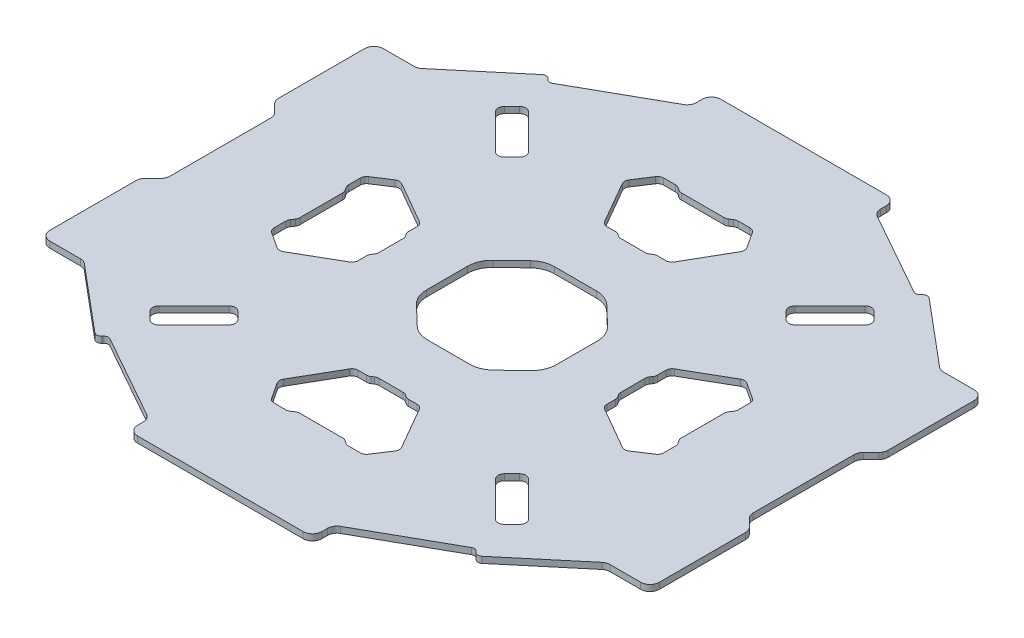
SolidWorks part; units mm, degrees
ref_plane "Piano frontale" through (0, 0, 0) normal (0, 0, 1) x (1, 0, 0)
ref_plane "Piano superiore" through (0, 0, 0) normal (0, 1, 0) x (1, 0, 0)
ref_plane "Piano destro" through (0, 0, 0) normal (1, 0, 0) x (0, 0, -1)
sketch "Schizzo3" plane through (0, 0, 0) normal (0, 1, 0) x (1, 0, 0)
  line L0 (-226.0625, 21.4509) -> (-226.0625, 53.9656)
  line L1 (-226.9412, 56.0869) -> (-229.4265, 58.5722)
  line L2 (-230.3052, 60.6935) -> (-230.3052, 88.4509)
  line L3 (-227.3052, 91.4509) -> (-217.3971, 91.4509)
  line L4 (-215.4687, 92.1528) -> (-194.4729, 109.7703)
  line L5 (-192.3597, 109.5854) -> (-192.1951, 109.3893)
  line L6 (-190.3111, 109.0459) -> (-163.2864, 124.2352)
  line L7 (-161.7563, 126.8504) -> (-161.7563, 128.7082)
  line L8 (-158.7563, 131.7082) -> (-105.3688, 131.7082)
  line L11 (-193.5625, 30.8043) -> (-193.5625, 44.6122)
  line L12 (-193.8889, 45.7071) -> (-194.5446, 46.7094)
  line L13 (-194.8709, 47.8043) -> (-194.8709, 51.6267)
  line L14 (-193.9658, 53.3003) -> (-188.7857, 56.689)
  line L15 (-186.6931, 56.7487) -> (-173.1597, 48.9588)
  line L16 (-172.1574, 47.2255) -> (-172.1574, 44.478)
  line L17 (-171.8311, 43.3831) -> (-171.3889, 42.7071)
  line L18 (-171.0625, 41.6122) -> (-171.0625, 33.8043)
  line L25 (-180.3244, 80.6668) -> (-191.6382, 91.9805)
  line L26 (-175.0211, 83.1417) -> (-177.496, 80.6668)
  line L27 (-186.3349, 97.2838) -> (-175.0211, 85.9701)
  line L28 (-191.6382, 94.809) -> (-189.1633, 97.2838)
  line L30 (-132.0625, 37.7082) -> (-218.4872, 124.1329) construction
  line L34 (-125.1586, 99.2082) -> (-138.9665, 99.2082)
  line L35 (-140.0614, 99.5346) -> (-141.0637, 100.1903)
  line L36 (-142.1586, 100.5166) -> (-145.981, 100.5166)
  line L37 (-147.6547, 99.6115) -> (-151.0433, 94.4314)
  line L38 (-151.103, 92.3388) -> (-143.3132, 78.8054)
  line L39 (-141.5798, 77.8031) -> (-138.8323, 77.8031)
  line L40 (-137.7374, 77.4768) -> (-137.0614, 77.0346)
  line L41 (-135.9665, 76.7082) -> (-128.1586, 76.7082)
  line L43 (-132.0625, 37.7082) -> (-45.6379, 124.1329) construction
  line L44 (-126.3877, 77.4768) -> (-127.0637, 77.0346)
  line L45 (-122.5453, 77.8031) -> (-125.2928, 77.8031)
  line L46 (-113.0221, 92.3388) -> (-120.8119, 78.8054)
  line L47 (-116.4704, 99.6115) -> (-113.0818, 94.4314)
  line L48 (-121.9665, 100.5166) -> (-118.1441, 100.5166)
  line L49 (-124.0637, 99.5346) -> (-123.0614, 100.1903)
  line L51 (-72.4869, 94.809) -> (-74.9618, 97.2838)
  line L52 (-77.7902, 97.2838) -> (-89.104, 85.9701)
  line L53 (-89.104, 83.1417) -> (-86.6291, 80.6668)
  line L54 (-83.8007, 80.6668) -> (-72.4869, 91.9805)
  line L55 (-93.0625, 41.6122) -> (-93.0625, 33.8043)
  line L56 (-92.294, 43.3831) -> (-92.7362, 42.7071)
  line L57 (-91.9677, 47.2255) -> (-91.9677, 44.478)
  line L58 (-77.432, 56.7487) -> (-90.9654, 48.9588)
  line L59 (-70.1593, 53.3003) -> (-75.3394, 56.689)
  line L60 (-69.2542, 47.8043) -> (-69.2542, 51.6267)
  line L61 (-70.2362, 45.7071) -> (-69.5805, 46.7094)
  line L62 (-70.5625, 30.8043) -> (-70.5625, 44.6122)
  line L63 (-102.3688, 126.8504) -> (-102.3688, 128.7082)
  line L64 (-73.814, 109.0459) -> (-100.8387, 124.2352)
  line L65 (-71.7654, 109.5854) -> (-71.93, 109.3893)
  line L66 (-48.6564, 92.1528) -> (-69.6522, 109.7703)
  line L67 (-36.8199, 91.4509) -> (-46.728, 91.4509)
  line L68 (-33.8199, 60.6935) -> (-33.8199, 88.4509)
  line L69 (-37.1839, 56.0869) -> (-34.6986, 58.5722)
  line L70 (-38.0625, 21.4509) -> (-38.0625, 53.9656)
  line L71 (-132.0625, 37.7082) -> (-45.6379, -48.7164) construction
  line L72 (-132.0625, 37.7082) -> (-218.4872, -48.7164) construction
  line L73 (-37.1839, 19.3296) -> (-34.6986, 16.8443)
  line L74 (-33.8199, 14.723) -> (-33.8199, -13.0344)
  line L75 (-36.8199, -16.0344) -> (-46.728, -16.0344)
  line L76 (-48.6564, -16.7363) -> (-69.6522, -34.3538)
  line L77 (-71.7654, -34.169) -> (-71.93, -33.9728)
  line L78 (-73.814, -33.6294) -> (-100.8387, -48.8187)
  line L79 (-102.3688, -51.4339) -> (-102.3688, -53.2918)
  line L80 (-70.2362, 29.7094) -> (-69.5805, 28.7071)
  line L81 (-69.2542, 27.6122) -> (-69.2542, 23.7898)
  line L82 (-70.1593, 22.1161) -> (-75.3394, 18.7275)
  line L83 (-77.432, 18.6678) -> (-90.9654, 26.4576)
  line L84 (-91.9677, 28.191) -> (-91.9677, 30.9385)
  line L85 (-92.294, 32.0334) -> (-92.7362, 32.7094)
  line L86 (-83.8007, -5.2503) -> (-72.4869, -16.5641)
  line L87 (-89.104, -7.7252) -> (-86.6291, -5.2503)
  line L88 (-77.7902, -21.8674) -> (-89.104, -10.5536)
  line L89 (-72.4869, -19.3925) -> (-74.9618, -21.8674)
  line L90 (-124.0637, -24.1181) -> (-123.0614, -24.7738)
  line L91 (-121.9665, -25.1001) -> (-118.1441, -25.1001)
  line L92 (-116.4704, -24.195) -> (-113.0818, -19.0149)
  line L93 (-113.0221, -16.9223) -> (-120.8119, -3.3889)
  line L94 (-122.5453, -2.3866) -> (-125.2928, -2.3866)
  line L95 (-126.3877, -2.0603) -> (-127.0637, -1.6181)
  line L96 (-132.0625, 37.7082) -> (-132.0625, 168.4992) construction
  line L97 (-135.9665, -1.2918) -> (-128.1586, -1.2918)
  line L98 (-137.7374, -2.0603) -> (-137.0614, -1.6181)
  line L99 (-141.5798, -2.3866) -> (-138.8323, -2.3866)
  line L100 (-151.103, -16.9223) -> (-143.3132, -3.3889)
  line L101 (-147.6547, -24.195) -> (-151.0433, -19.0149)
  line L102 (-142.1586, -25.1001) -> (-145.981, -25.1001)
  line L103 (-140.0614, -24.1181) -> (-141.0637, -24.7738)
  line L104 (-125.1586, -23.7918) -> (-138.9665, -23.7918)
  line L105 (-191.6382, -19.3925) -> (-189.1633, -21.8674)
  line L106 (-186.3349, -21.8674) -> (-175.0211, -10.5536)
  line L107 (-175.0211, -7.7252) -> (-177.496, -5.2503)
  line L108 (-180.3244, -5.2503) -> (-191.6382, -16.5641)
  line L109 (-171.8311, 32.0334) -> (-171.3889, 32.7094)
  line L110 (-172.1574, 28.191) -> (-172.1574, 30.9385)
  line L111 (-186.6931, 18.6678) -> (-173.1597, 26.4576)
  line L112 (-193.9658, 22.1161) -> (-188.7857, 18.7275)
  line L113 (-194.8709, 27.6122) -> (-194.8709, 23.7898)
  line L114 (-193.8889, 29.7094) -> (-194.5446, 28.7071)
  line L115 (-158.7563, -56.2918) -> (-105.3688, -56.2918)
  line L116 (-161.7563, -51.4339) -> (-161.7563, -53.2918)
  line L117 (-190.3111, -33.6294) -> (-163.2864, -48.8187)
  line L118 (-192.3597, -34.169) -> (-192.1951, -33.9728)
  line L119 (-215.4687, -16.7363) -> (-194.4729, -34.3538)
  line L120 (-227.3052, -16.0344) -> (-217.3971, -16.0344)
  line L121 (-230.3052, 14.723) -> (-230.3052, -13.0344)
  line L122 (-226.9412, 19.3296) -> (-229.4265, 16.8443)
  line L123 (-132.0625, 168.4992) -> (-132.0625, -119.8545) construction
  line L124 (-132.0625, 37.7082) -> (44.6904, 37.7082) construction
  line L125 (44.6904, 37.7082) -> (-300.9787, 37.7082) construction
  line L127 (-152.9671, 31.1216) -> (-152.9671, 44.2949)
  line L128 (-150.5029, 50.0702) -> (-144.3835, 55.9358)
  line L129 (-138.8476, 58.1605) -> (-125.2775, 58.1605)
  line L131 (-113.6222, 50.0702) -> (-119.7416, 55.9358)
  line L132 (-111.158, 31.1216) -> (-111.158, 44.2949)
  line L133 (-150.5029, 25.3463) -> (-144.3835, 19.4806)
  line L134 (-113.6222, 25.3463) -> (-119.7416, 19.4806)
  line L135 (-138.8476, 17.256) -> (-125.2775, 17.256)
  arc A0 (-161.7563, 128.7082) -> (-158.7563, 131.7082) centre (-158.7563, 128.7082) cw
  arc A1 (-163.2864, 124.2352) -> (-161.7563, 126.8504) centre (-164.7563, 126.8504) ccw
  arc A2 (-217.3971, 91.4509) -> (-215.4687, 92.1528) centre (-217.3971, 94.4509) ccw
  arc A3 (-230.3052, 88.4509) -> (-227.3052, 91.4509) centre (-227.3052, 88.4509) cw
  arc A4 (-226.0625, 53.9656) -> (-226.9412, 56.0869) centre (-229.0625, 53.9656) ccw
  arc A5 (-229.4265, 58.5722) -> (-230.3052, 60.6935) centre (-227.3052, 60.6935) cw
  arc A6 (-192.1951, 109.3893) -> (-190.3111, 109.0459) centre (-191.046, 110.3535) ccw
  arc A7 (-194.4729, 109.7703) -> (-192.3597, 109.5854) centre (-193.5087, 108.6213) cw
  arc A8 (-175.0211, 83.1417) -> (-175.0211, 85.9701) centre (-176.4354, 84.5559) ccw
  arc A9 (-180.3244, 80.6668) -> (-177.496, 80.6668) centre (-178.9102, 82.0811) ccw
  arc A10 (-186.3349, 97.2838) -> (-189.1633, 97.2838) centre (-187.7491, 95.8696) ccw
  arc A11 (-191.6382, 91.9805) -> (-191.6382, 94.809) centre (-190.2239, 93.3948) cw
  arc A12 (-171.3889, 42.7071) -> (-171.0625, 41.6122) centre (-173.0625, 41.6122) cw
  arc A13 (-172.1574, 44.478) -> (-171.8311, 43.3831) centre (-170.1574, 44.478) ccw
  arc A14 (-173.1597, 48.9588) -> (-172.1574, 47.2255) centre (-174.1574, 47.2255) cw
  arc A15 (-188.7857, 56.689) -> (-186.6931, 56.7487) centre (-187.6908, 55.0153) cw
  arc A16 (-193.5625, 44.6122) -> (-193.8889, 45.7071) centre (-195.5625, 44.6122) ccw
  arc A17 (-194.5446, 46.7094) -> (-194.8709, 47.8043) centre (-192.8709, 47.8043) cw
  arc A18 (-194.8709, 51.6267) -> (-193.9658, 53.3003) centre (-192.8709, 51.6267) cw
  arc A19 (-137.0614, 77.0346) -> (-135.9665, 76.7082) centre (-135.9665, 78.7082) ccw
  arc A20 (-138.8323, 77.8031) -> (-137.7374, 77.4768) centre (-138.8323, 75.8031) cw
  arc A21 (-143.3132, 78.8054) -> (-141.5798, 77.8031) centre (-141.5798, 79.8031) ccw
  arc A22 (-138.9665, 99.2082) -> (-140.0614, 99.5346) centre (-138.9665, 101.2082) cw
  arc A23 (-141.0637, 100.1903) -> (-142.1586, 100.5166) centre (-142.1586, 98.5166) ccw
  arc A24 (-145.981, 100.5166) -> (-147.6547, 99.6115) centre (-145.981, 98.5166) ccw
  arc A25 (-151.0433, 94.4314) -> (-151.103, 92.3388) centre (-149.3696, 93.3365) ccw
  arc A26 (-113.0818, 94.4314) -> (-113.0221, 92.3388) centre (-114.7555, 93.3365) cw
  arc A27 (-118.1441, 100.5166) -> (-116.4704, 99.6115) centre (-118.1441, 98.5166) cw
  arc A28 (-123.0614, 100.1903) -> (-121.9665, 100.5166) centre (-121.9665, 98.5166) cw
  arc A29 (-125.1586, 99.2082) -> (-124.0637, 99.5346) centre (-125.1586, 101.2082) ccw
  arc A30 (-120.8119, 78.8054) -> (-122.5453, 77.8031) centre (-122.5453, 79.8031) cw
  arc A31 (-125.2928, 77.8031) -> (-126.3877, 77.4768) centre (-125.2928, 75.8031) ccw
  arc A32 (-127.0637, 77.0346) -> (-128.1586, 76.7082) centre (-128.1586, 78.7082) cw
  arc A33 (-69.2542, 51.6267) -> (-70.1593, 53.3003) centre (-71.2542, 51.6267) ccw
  arc A34 (-69.5805, 46.7094) -> (-69.2542, 47.8043) centre (-71.2542, 47.8043) ccw
  arc A35 (-70.5625, 44.6122) -> (-70.2362, 45.7071) centre (-68.5625, 44.6122) cw
  arc A36 (-75.3394, 56.689) -> (-77.432, 56.7487) centre (-76.4343, 55.0153) ccw
  arc A37 (-90.9654, 48.9588) -> (-91.9677, 47.2255) centre (-89.9677, 47.2255) ccw
  arc A38 (-91.9677, 44.478) -> (-92.294, 43.3831) centre (-93.9677, 44.478) cw
  arc A39 (-92.7362, 42.7071) -> (-93.0625, 41.6122) centre (-91.0625, 41.6122) ccw
  arc A40 (-72.4869, 91.9805) -> (-72.4869, 94.809) centre (-73.9012, 93.3948) ccw
  arc A41 (-77.7902, 97.2838) -> (-74.9618, 97.2838) centre (-76.376, 95.8696) cw
  arc A42 (-83.8007, 80.6668) -> (-86.6291, 80.6668) centre (-85.2149, 82.0811) cw
  arc A43 (-89.104, 83.1417) -> (-89.104, 85.9701) centre (-87.6897, 84.5559) cw
  arc A44 (-69.6522, 109.7703) -> (-71.7654, 109.5854) centre (-70.6164, 108.6213) ccw
  arc A45 (-71.93, 109.3893) -> (-73.814, 109.0459) centre (-73.0791, 110.3535) cw
  arc A46 (-34.6986, 58.5722) -> (-33.8199, 60.6935) centre (-36.8199, 60.6935) ccw
  arc A47 (-38.0625, 53.9656) -> (-37.1839, 56.0869) centre (-35.0625, 53.9656) cw
  arc A48 (-33.8199, 88.4509) -> (-36.8199, 91.4509) centre (-36.8199, 88.4509) ccw
  arc A49 (-46.728, 91.4509) -> (-48.6564, 92.1528) centre (-46.728, 94.4509) cw
  arc A50 (-100.8387, 124.2352) -> (-102.3688, 126.8504) centre (-99.3688, 126.8504) cw
  arc A51 (-102.3688, 128.7082) -> (-105.3688, 131.7082) centre (-105.3688, 128.7082) ccw
  arc A52 (-102.3688, -53.2918) -> (-105.3688, -56.2918) centre (-105.3688, -53.2918) cw
  arc A53 (-100.8387, -48.8187) -> (-102.3688, -51.4339) centre (-99.3688, -51.4339) ccw
  arc A54 (-46.728, -16.0344) -> (-48.6564, -16.7363) centre (-46.728, -19.0344) ccw
  arc A55 (-33.8199, -13.0344) -> (-36.8199, -16.0344) centre (-36.8199, -13.0344) cw
  arc A56 (-38.0625, 21.4509) -> (-37.1839, 19.3296) centre (-35.0625, 21.4509) ccw
  arc A57 (-34.6986, 16.8443) -> (-33.8199, 14.723) centre (-36.8199, 14.723) cw
  arc A58 (-71.93, -33.9728) -> (-73.814, -33.6294) centre (-73.0791, -34.937) ccw
  arc A59 (-69.6522, -34.3538) -> (-71.7654, -34.169) centre (-70.6164, -33.2048) cw
  arc A60 (-89.104, -7.7252) -> (-89.104, -10.5536) centre (-87.6897, -9.1394) ccw
  arc A61 (-83.8007, -5.2503) -> (-86.6291, -5.2503) centre (-85.2149, -6.6646) ccw
  arc A62 (-77.7902, -21.8674) -> (-74.9618, -21.8674) centre (-76.376, -20.4531) ccw
  arc A63 (-72.4869, -16.5641) -> (-72.4869, -19.3925) centre (-73.9012, -17.9783) cw
  arc A64 (-92.7362, 32.7094) -> (-93.0625, 33.8043) centre (-91.0625, 33.8043) cw
  arc A65 (-91.9677, 30.9385) -> (-92.294, 32.0334) centre (-93.9677, 30.9385) ccw
  arc A66 (-90.9654, 26.4576) -> (-91.9677, 28.191) centre (-89.9677, 28.191) cw
  arc A67 (-75.3394, 18.7275) -> (-77.432, 18.6678) centre (-76.4343, 20.4012) cw
  arc A68 (-70.5625, 30.8043) -> (-70.2362, 29.7094) centre (-68.5625, 30.8043) ccw
  arc A69 (-69.5805, 28.7071) -> (-69.2542, 27.6122) centre (-71.2542, 27.6122) cw
  arc A70 (-69.2542, 23.7898) -> (-70.1593, 22.1161) centre (-71.2542, 23.7898) cw
  arc A71 (-127.0637, -1.6181) -> (-128.1586, -1.2918) centre (-128.1586, -3.2918) ccw
  arc A72 (-125.2928, -2.3866) -> (-126.3877, -2.0603) centre (-125.2928, -0.3866) cw
  arc A73 (-120.8119, -3.3889) -> (-122.5453, -2.3866) centre (-122.5453, -4.3866) ccw
  arc A74 (-125.1586, -23.7918) -> (-124.0637, -24.1181) centre (-125.1586, -25.7918) cw
  arc A75 (-123.0614, -24.7738) -> (-121.9665, -25.1001) centre (-121.9665, -23.1001) ccw
  arc A76 (-118.1441, -25.1001) -> (-116.4704, -24.195) centre (-118.1441, -23.1001) ccw
  arc A77 (-113.0818, -19.0149) -> (-113.0221, -16.9223) centre (-114.7555, -17.92) ccw
  arc A78 (-151.0433, -19.0149) -> (-151.103, -16.9223) centre (-149.3696, -17.92) cw
  arc A79 (-145.981, -25.1001) -> (-147.6547, -24.195) centre (-145.981, -23.1001) cw
  arc A80 (-141.0637, -24.7738) -> (-142.1586, -25.1001) centre (-142.1586, -23.1001) cw
  arc A81 (-138.9665, -23.7918) -> (-140.0614, -24.1181) centre (-138.9665, -25.7918) ccw
  arc A82 (-143.3132, -3.3889) -> (-141.5798, -2.3866) centre (-141.5798, -4.3866) cw
  arc A83 (-138.8323, -2.3866) -> (-137.7374, -2.0603) centre (-138.8323, -0.3866) ccw
  arc A84 (-137.0614, -1.6181) -> (-135.9665, -1.2918) centre (-135.9665, -3.2918) cw
  arc A85 (-194.8709, 23.7898) -> (-193.9658, 22.1161) centre (-192.8709, 23.7898) ccw
  arc A86 (-194.5446, 28.7071) -> (-194.8709, 27.6122) centre (-192.8709, 27.6122) ccw
  arc A87 (-193.5625, 30.8043) -> (-193.8889, 29.7094) centre (-195.5625, 30.8043) cw
  arc A88 (-188.7857, 18.7275) -> (-186.6931, 18.6678) centre (-187.6908, 20.4012) ccw
  arc A89 (-173.1597, 26.4576) -> (-172.1574, 28.191) centre (-174.1574, 28.191) ccw
  arc A90 (-172.1574, 30.9385) -> (-171.8311, 32.0334) centre (-170.1574, 30.9385) cw
  arc A91 (-171.3889, 32.7094) -> (-171.0625, 33.8043) centre (-173.0625, 33.8043) ccw
  arc A92 (-191.6382, -16.5641) -> (-191.6382, -19.3925) centre (-190.2239, -17.9783) ccw
  arc A93 (-186.3349, -21.8674) -> (-189.1633, -21.8674) centre (-187.7491, -20.4531) cw
  arc A94 (-180.3244, -5.2503) -> (-177.496, -5.2503) centre (-178.9102, -6.6646) cw
  arc A95 (-175.0211, -7.7252) -> (-175.0211, -10.5536) centre (-176.4354, -9.1394) cw
  arc A96 (-194.4729, -34.3538) -> (-192.3597, -34.169) centre (-193.5087, -33.2048) ccw
  arc A97 (-192.1951, -33.9728) -> (-190.3111, -33.6294) centre (-191.046, -34.937) cw
  arc A98 (-229.4265, 16.8443) -> (-230.3052, 14.723) centre (-227.3052, 14.723) ccw
  arc A99 (-226.0625, 21.4509) -> (-226.9412, 19.3296) centre (-229.0625, 21.4509) cw
  arc A100 (-230.3052, -13.0344) -> (-227.3052, -16.0344) centre (-227.3052, -13.0344) ccw
  arc A101 (-217.3971, -16.0344) -> (-215.4687, -16.7363) centre (-217.3971, -19.0344) cw
  arc A102 (-163.2864, -48.8187) -> (-161.7563, -51.4339) centre (-164.7563, -51.4339) cw
  arc A103 (-161.7563, -53.2918) -> (-158.7563, -56.2918) centre (-158.7563, -53.2918) ccw
  arc A112 (-152.9671, 44.2949) -> (-150.5029, 50.0702) centre (-144.9671, 44.2949) cw
  arc A113 (-125.2775, 58.1605) -> (-119.7416, 55.9358) centre (-125.2775, 50.1605) cw
  arc A114 (-111.158, 31.1216) -> (-113.6222, 25.3463) centre (-119.158, 31.1216) cw
  arc A115 (-138.8476, 17.256) -> (-144.3835, 19.4806) centre (-138.8476, 25.256) cw
  arc A116 (-152.9671, 31.1216) -> (-150.5029, 25.3463) centre (-144.9671, 31.1216) ccw
  arc A117 (-144.3835, 55.9358) -> (-138.8476, 58.1605) centre (-138.8476, 50.1605) cw
  arc A118 (-113.6222, 50.0702) -> (-111.158, 44.2949) centre (-119.158, 44.2949) cw
  arc A119 (-119.7416, 19.4806) -> (-125.2775, 17.256) centre (-125.2775, 25.256) cw
  point P13 (-176.2586, 81.9043)
  point P61 (-171.0625, 42.2082)
  point P64 (-172.1574, 43.8819)
  point P67 (-172.1574, 48.3819)
  point P70 (-187.7577, 57.3615)
  point P73 (-193.5625, 45.2082)
  point P76 (-194.8709, 47.2082)
  point P79 (-194.8709, 52.7082)
  point P82 (-136.5625, 76.7082)
  point P85 (-138.2362, 77.8031)
  point P88 (-142.7362, 77.8031)
  point P91 (-139.5625, 99.2082)
  point P94 (-141.5625, 100.5166)
  point P97 (-147.0625, 100.5166)
  point P100 (-151.7158, 93.4034)
  point P183 (-112.4093, 93.4034)
  point P184 (-117.0625, 100.5166)
  point P185 (-122.5625, 100.5166)
  point P186 (-124.5625, 99.2082)
  point P187 (-121.3889, 77.8031)
  point P188 (-125.8889, 77.8031)
  point P189 (-127.5625, 76.7082)
  point P190 (-69.2542, 52.7082)
  point P191 (-69.2542, 47.2082)
  point P192 (-70.5625, 45.2082)
  point P193 (-76.3674, 57.3615)
  point P194 (-91.9677, 48.3819)
  point P195 (-91.9677, 43.8819)
  point P196 (-93.0625, 42.2082)
  point P197 (-87.8665, 81.9043)
  point P357 (-142.0625, 58.1605)
  point P359 (-87.8665, -6.4878)
  point P360 (-93.0625, 33.2082)
  point P361 (-91.9677, 31.5346)
  point P362 (-91.9677, 27.0346)
  point P363 (-76.3674, 18.055)
  point P364 (-70.5625, 30.2082)
  point P365 (-69.2542, 28.2082)
  point P366 (-69.2542, 22.7082)
  point P367 (-127.5625, -1.2918)
  point P368 (-125.8889, -2.3866)
  point P369 (-121.3889, -2.3866)
  point P370 (-124.5625, -23.7918)
  point P371 (-122.5625, -25.1001)
  point P372 (-117.0625, -25.1001)
  point P373 (-112.4093, -17.9869)
  point P374 (-151.7158, -17.9869)
  point P375 (-147.0625, -25.1001)
  point P376 (-141.5625, -25.1001)
  point P377 (-139.5625, -23.7918)
  point P378 (-142.7362, -2.3866)
  point P379 (-138.2362, -2.3866)
  point P380 (-136.5625, -1.2918)
  point P381 (-194.8709, 22.7082)
  point P382 (-194.8709, 28.2082)
  point P383 (-193.5625, 30.2082)
  point P384 (-187.7577, 18.055)
  point P385 (-172.1574, 27.0346)
  point P386 (-172.1574, 31.5346)
  point P387 (-171.0625, 33.2082)
  point P388 (-176.2586, -6.4878)
  point P394 (-152.9671, 47.7082)
  point P397 (-152.9671, 27.7082)
  point P400 (-142.0625, 17.256)
  point P403 (-122.0625, 17.256)
  point P406 (-111.158, 27.7082)
  point P409 (-111.158, 47.7082)
  point P412 (-122.0625, 58.1605)
  dimension "D2" = 3
  dimension "D3" = 1.5
  dimension "D4" = 2
  dimension "D5" = 2
  dimension "D6" = 2
  dimension "D7" = 8
  dimension "D8" = 8
extrude "Estrusione-Estrusione1" add sketch "Schizzo3" along normal blind 2
